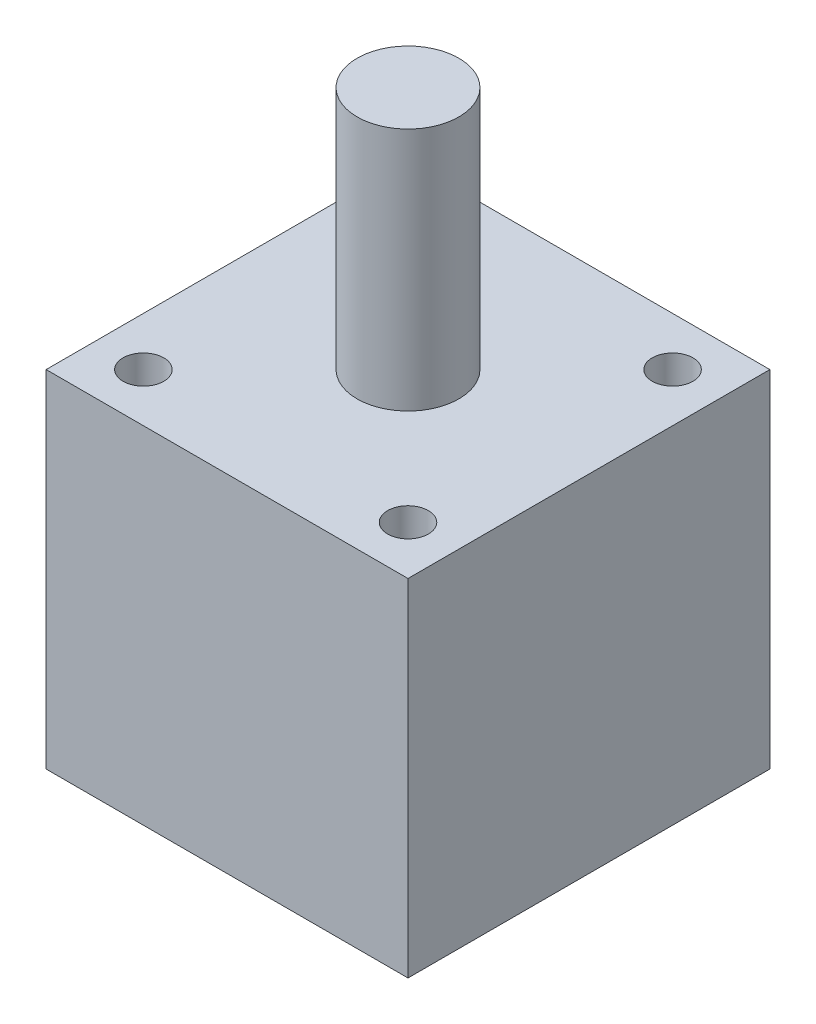
SolidWorks part; units mm, degrees
ref_plane "Front Plane" through (0, 0, 0) normal (0, 0, 1) x (1, 0, 0)
ref_plane "Top Plane" through (0, 0, 0) normal (0, 1, 0) x (1, 0, 0)
ref_plane "Right Plane" through (0, 0, 0) normal (1, 0, 0) x (0, 0, -1)
sketch "Sketch1" plane through (0, 0, 0) normal (0, 1, 0) x (1, 0, 0)
  line L1 (-17.78, -17.78) -> (17.78, -17.78)
  line L2 (-17.78, -17.78) -> (-17.78, 17.78)
  line L3 (-17.78, 17.78) -> (17.78, 17.78)
  line L4 (17.78, -17.78) -> (17.78, 17.78)
  line L5 (-17.78, -17.78) -> (17.78, 17.78) construction
  line L6 (-17.78, 17.78) -> (17.78, -17.78) construction
  point P0 (0, 0)
  dimension "D1" = 35.56
extrude "Boss-Extrude1" add sketch "Sketch1" along normal blind 34
sketch "Sketch2" plane through (0, 34, 0) normal (0, 1, 0) x (1, 0, 0)
  circle A0 centre (0, 0) radius 5
extrude "Boss-Extrude2" add sketch "Sketch2" along normal blind 24
sketch "Sketch3" plane through (0, 0, 0) normal (0, -1, 0) x (1, 0, 0)
  circle A0 centre (0, 0) radius 5
extrude "Boss-Extrude3" add sketch "Sketch3" along normal blind 12
sketch "Sketch4" plane through (0, 34, 0) normal (0, 1, 0) x (1, 0, 0)
  line L1 (-13, 13) -> (13, 13) construction
  line L2 (-13, 13) -> (-13, -13) construction
  line L3 (-13, -13) -> (13, -13) construction
  line L4 (13, 13) -> (13, -13) construction
  circle A0 centre (-13, 13) radius 2
  circle A1 centre (13, 13) radius 2
  circle A2 centre (13, -13) radius 2
  circle A3 centre (-13, -13) radius 2
  point P4 (0, 13)
  point P6 (-13, 0)
  dimension "D2" = 4
  dimension "D1" = 26
extrude "Cut-Extrude1" cut sketch "Sketch4" against normal up to surface (34 mm away) up to face at (0, 0, -5)
